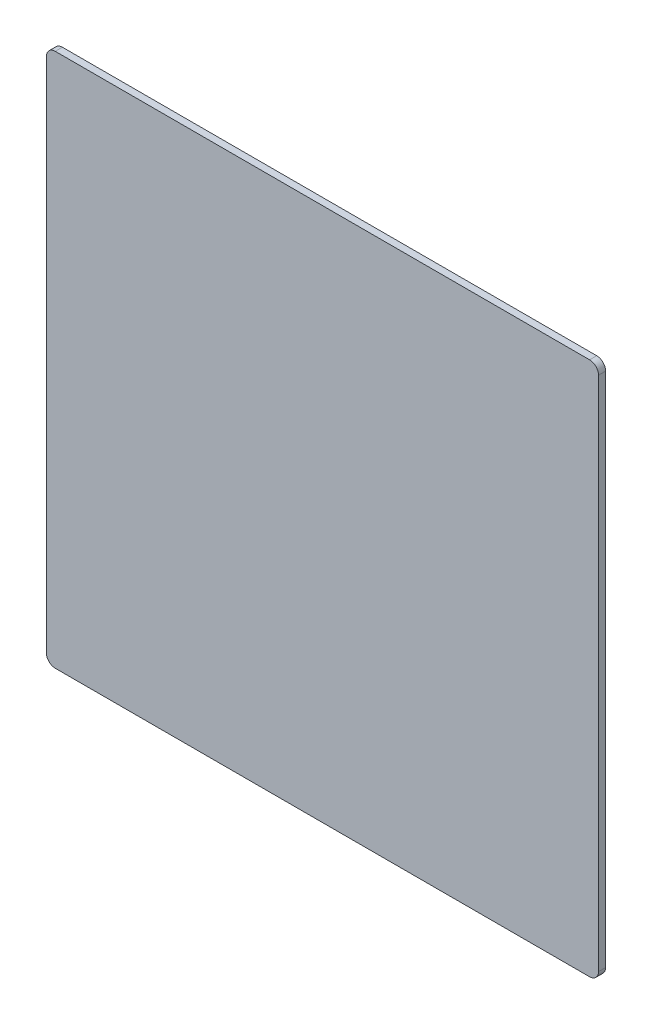
SolidWorks part; units mm, degrees
material "ﾎﾟﾘｶｰﾎﾞﾈｰﾄ(PC)高粘度"
ref_plane "正面" through (0, 0, 0) normal (0, 0, 1) x (1, 0, 0)
ref_plane "平面" through (0, 0, 0) normal (0, 1, 0) x (1, 0, 0)
ref_plane "右側面" through (0, 0, 0) normal (1, 0, 0) x (0, 0, -1)
sketch "ｽｹｯﾁ1" plane through (0, 0, 0) normal (0, 0, 1) x (1, 0, 0)
  line L1 (-155, -150) -> (155, -150)
  line L2 (-155, -150) -> (-155, 150)
  line L3 (-155, 150) -> (155, 150)
  line L4 (155, -150) -> (155, 150)
  line L5 (-155, -150) -> (155, 150) construction
  line L6 (-155, 150) -> (155, -150) construction
  point P0 (0, 0)
  dimension "D1" = 310
  dimension "D2" = 300
extrude "ﾎﾞｽ - 押し出し1" add sketch "ｽｹｯﾁ1" along normal blind 4
fillet "ﾌｨﾚｯﾄ1" radius 5 4 edges at (155, -150, 2) (155, 150, 2) (-155, 150, 2) (-155, -150, 2)
